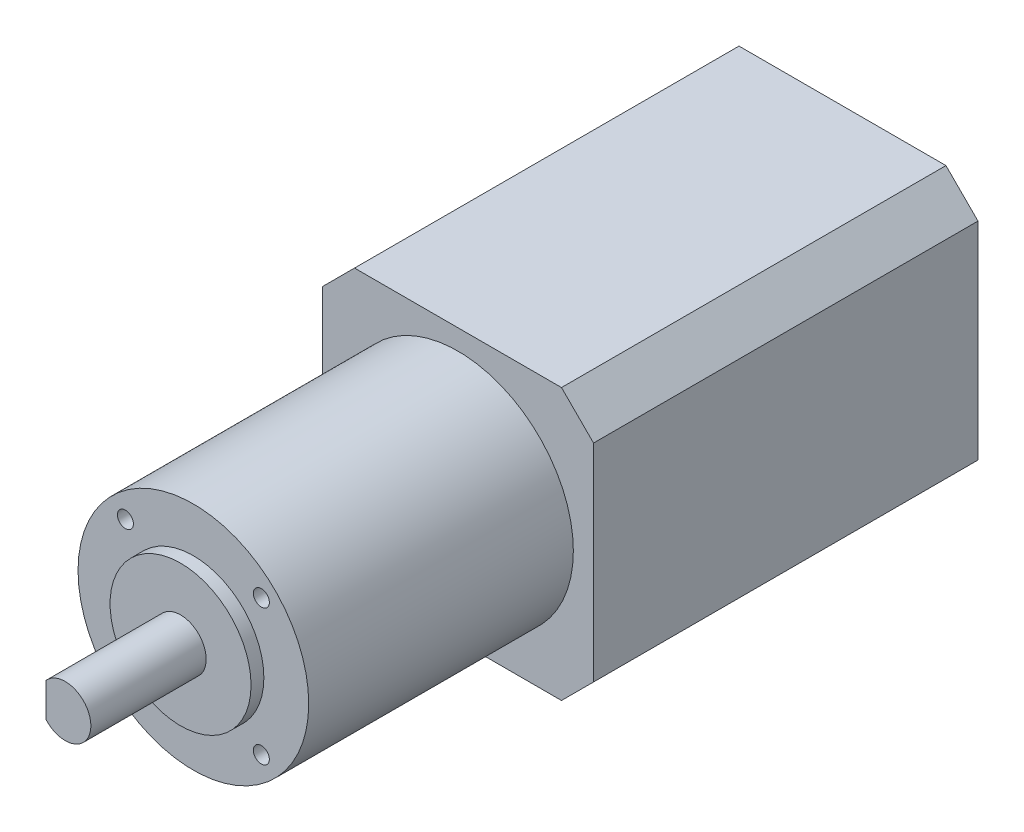
SolidWorks part; units mm, degrees
ref_plane "前视基准面" through (0, 0, 0) normal (0, 0, 1) x (1, 0, 0)
ref_plane "上视基准面" through (0, 0, 0) normal (0, 1, 0) x (1, 0, 0)
ref_plane "右视基准面" through (0, 0, 0) normal (1, 0, 0) x (0, 0, -1)
sketch "草图1" plane through (0, 0, 0) normal (0, 0, 1) x (1, 0, 0)
  line L0 (-21.15, 16.15) -> (-16.15, 21.15)
  line L1 (-16.15, -21.15) -> (16.15, -21.15)
  line L2 (-21.15, -16.15) -> (-21.15, 16.15)
  line L3 (-16.15, 21.15) -> (16.15, 21.15)
  line L4 (21.15, -16.15) -> (21.15, 16.15)
  line L5 (-21.15, -21.15) -> (21.15, 21.15) construction
  line L6 (-21.15, 21.15) -> (21.15, -21.15) construction
  line L7 (16.15, 21.15) -> (21.15, 16.15)
  line L8 (-21.15, -16.15) -> (-16.15, -21.15)
  line L9 (16.15, -21.15) -> (21.15, -16.15)
  point P0 (0, 0)
  dimension "D1" = 42.3
extrude "凸台-拉伸1" add sketch "草图1" along normal blind 60
sketch "草图2" plane through (0, 0, 60) normal (0, 0, 1) x (1, 0, 0)
  circle A0 centre (0, 0) radius 18
  dimension "D1" = 36
extrude "凸台-拉伸2" add sketch "草图2" along normal blind 41.3
sketch "草图3" plane through (0, 0, 101.3) normal (0, 0, 1) x (1, 0, 0)
  circle A0 centre (0, 0) radius 11
  dimension "D1" = 22
extrude "凸台-拉伸3" add sketch "草图3" along normal blind 2
sketch "草图4" plane through (0, 0, 103.3) normal (0, 0, 1) x (1, 0, 0)
  circle A0 centre (0, 0) radius 4
  dimension "D1" = 8
extrude "凸台-拉伸4" add sketch "草图4" along normal blind 18
sketch "草图5" plane through (0, 0, 121.3) normal (0, 0, 1) x (1, 0, 0)
  line L0 (-3, 5.3779) -> (-3, -8.0729)
  line L1 (-3, -8.0729) -> (-11.0943, -8.0729)
  line L2 (-11.0943, -8.0729) -> (-11.0943, 5.3779)
  line L3 (-11.0943, 5.3779) -> (-3, 5.3779)
  dimension "D1" = 3
extrude "切除-拉伸1" cut sketch "草图5" against normal blind 15
sketch "草图6" plane through (0, 0, 101.3) normal (0, 0, 1) x (1, 0, 0)
  line L0 (-10.6066, 10.6066) -> (10.6066, 10.6066) construction
  line L1 (10.6066, 10.6066) -> (10.6066, -10.6066) construction
  line L2 (10.6066, -10.6066) -> (-10.6066, -10.6066) construction
  line L3 (-10.6066, -10.6066) -> (-10.6066, 10.6066) construction
  line L4 (-10.6066, 10.6066) -> (10.6066, -10.6066) construction
  circle A0 centre (-10.6066, 10.6066) radius 1
  circle A1 centre (10.6066, 10.6066) radius 1
  circle A2 centre (-10.6066, -10.6066) radius 1
  circle A3 centre (10.6066, -10.6066) radius 1
  dimension "D2" = 2
  dimension "D1" = 30
extrude "切除-拉伸2" cut sketch "草图6" against normal blind 5
hole_wizard "M3 螺纹孔1" positions "草图7" profile "草图8" tap size "M3" standard "GB"
sketch "草图7" plane through (0, 0, 101.3) normal (0, 0, 1) x (1, 0, 0)
  point P0 (-10.6066, 10.6066)
  point P3 (10.6066, 10.6066)
  point P6 (-10.6066, -10.6066)
  point P9 (10.6066, -10.6066)
sketch "草图8" plane through (-10.6066, 10.6066, 101.3) normal (1, 0, 0) x (0, -1, 0)
  line L0 (0, 0) -> (0, 8.2511)
  line L1 (0, 8.2511) -> (1.25, 7.5)
  line L2 (1.25, 7.5) -> (1.25, 0)
  line L5 (1.25, 0) -> (0, 0)
  line L10 (0, 8.2511) -> (-1.25, 7.5) construction
  line L11 (0, -6.35) -> (0, 107.95) construction
  dimension "螺纹孔钻头直径" = 2.5
  dimension "螺纹孔钻头深度" = 7.5
  dimension "导头角度" = 118
cosmetic thread "孔螺蚊线1" parameters "D1"=6, "D2"=3
cosmetic thread "孔螺蚊线2" parameters "D1"=6, "D2"=3
cosmetic thread "孔螺蚊线3" parameters "D1"=6, "D2"=3
cosmetic thread "孔螺蚊线4" parameters "D1"=6, "D2"=3
